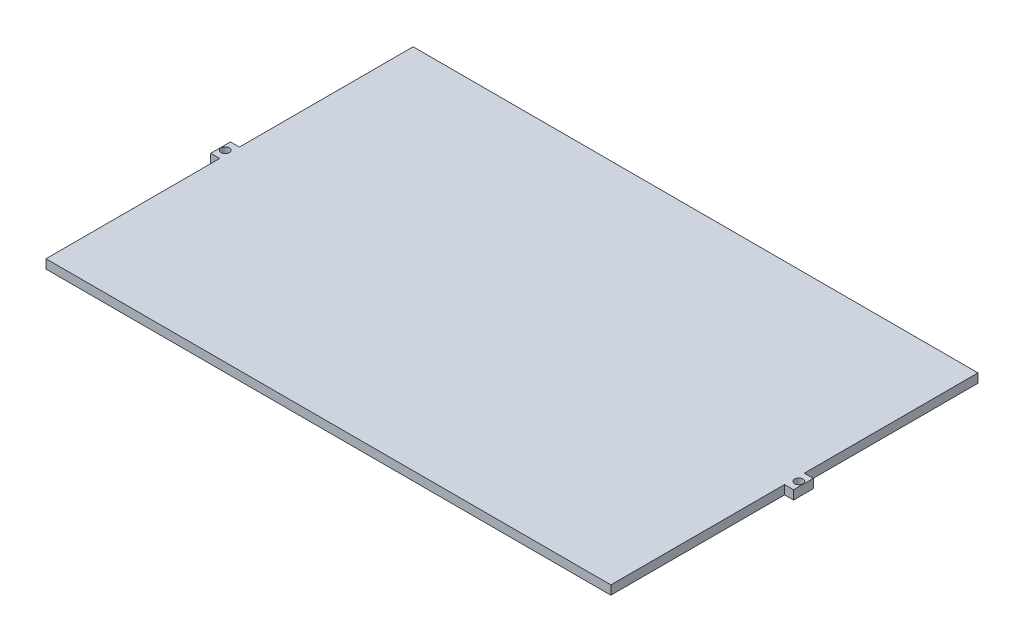
SolidWorks part; units mm, degrees
ref_plane "Front Plane" through (0, 0, 0) normal (0, 0, 1) x (1, 0, 0)
ref_plane "Top Plane" through (0, 0, 0) normal (0, 1, 0) x (1, 0, 0)
ref_plane "Right Plane" through (0, 0, 0) normal (1, 0, 0) x (0, 0, -1)
sketch "Sketch2" plane through (0, 0, 0) normal (0, 1, 0) x (1, 0, 0)
  line L1 (-100, 65) -> (100, 65)
  line L2 (-100, 65) -> (-100, -65)
  line L3 (-100, -65) -> (100, -65)
  line L4 (100, 65) -> (100, -65)
  line L5 (-100, 65) -> (100, -65) construction
  line L6 (-100, -65) -> (100, 65) construction
  point P0 (0, 0)
  dimension "D1" = 200
  dimension "D2" = 130
extrude "Boss-Extrude1" add sketch "Sketch2" along normal blind 3.18
sketch "Sketch5" plane through (-100, 0, 0) normal (-1, 0, 0) x (0, 0, 1)
  line L0 (0, 0) -> (0, 3.18) construction
  line L1 (-65, 0) -> (65, 0) construction
  line L2 (-65, 3.18) -> (65, 3.18) construction
  line L5 (3.5, 0) -> (-3.5, 0)
  line L6 (3.5, 0) -> (3.5, 3.18)
  line L7 (3.5, 3.18) -> (-3.5, 3.18)
  line L8 (-3.5, 0) -> (-3.5, 3.18)
  line L9 (3.5, 0) -> (-3.5, 3.18) construction
  line L10 (3.5, 3.18) -> (-3.5, 0) construction
  point P6 (0, 1.59)
  dimension "D1" = 7
sketch "Sketch7" [suppressed] plane through (0, 0, -65) normal (0, 0, -1) x (-1, 0, 0)
  line L0 (3.5, 0) -> (3.5, 3.18)
  line L1 (3.5, 0) -> (-3.5, 0)
  line L2 (3.5, 3.18) -> (-3.5, 3.18)
  line L3 (-3.5, 0) -> (-3.5, 3.18)
  line L4 (-65, 0) -> (65, 0) construction
  line L5 (-65, 3.18) -> (65, 3.18) construction
  line L7 (65, 3.18) -> (65, 0) construction
  line L8 (-65, 3.18) -> (-65, 0) construction
  line L9 (0, 0) -> (0, 3.18) construction
  dimension "D1" = 7
  dimension "D2" = 3.5
extrude "Cut-Extrude2" [suppressed] cut sketch "Sketch7" against normal blind 3.18
sketch "Sketch8" [suppressed] plane through (0, 0, -61.82) normal (0, 0, -1) x (-1, 0, 0)
  line L0 (0, 0) -> (0, 3.18) construction
  line L1 (-3.5, 0) -> (3.5, 0) construction
  line L2 (3.5, 3.18) -> (-3.5, 3.18) construction
  line L4 (-1.47, 0) -> (1.47, 0)
  line L5 (-1.47, 0) -> (-1.47, 3.18)
  line L6 (-1.47, 3.18) -> (1.47, 3.18)
  line L7 (1.47, 0) -> (1.47, 3.18)
  line L8 (-1.47, 0) -> (1.47, 3.18) construction
  line L9 (-1.47, 3.18) -> (1.47, 0) construction
  point P6 (0, 1.59)
  dimension "D1" = 2.94
extrude "Cut-Extrude3" [suppressed] cut sketch "Sketch8" against normal blind 2.08
sketch "Sketch9" [suppressed] plane through (0, 3.18, 0) normal (0, 1, 0) x (1, 0, 0)
  line L4 (0, 60.1231) -> (0, 52.805) construction
  line L5 (3.25, 57.14) -> (-3.25, 57.14)
  line L6 (3.25, 57.14) -> (3.25, 59.74)
  line L7 (3.25, 59.74) -> (-3.25, 59.74)
  line L8 (-3.25, 57.14) -> (-3.25, 59.74)
  line L10 (-1.47, 59.74) -> (1.47, 59.74) construction
  dimension "D1" = 0
  dimension "D2" = 6.5
  dimension "D3" = 3.25
  dimension "D4" = 2.6
extrude "Cut-Extrude4" [suppressed] cut sketch "Sketch9" against normal through all
sketch "Sketch10" [suppressed] plane through (0, 0, -57.14) normal (0, 0, -1) x (-1, 0, 0)
  line L0 (3.25, 0) -> (-3.25, 0) construction
  line L1 (-1.3107, 0) -> (1.6293, 0)
  line L2 (-1.3107, 0) -> (-1.3107, 3.18)
  line L3 (-1.3107, 3.18) -> (1.6293, 3.18)
  line L4 (1.6293, 0) -> (1.6293, 3.18)
  line L5 (3.25, 3.18) -> (-3.25, 3.18) construction
  dimension "D1" = 2.94
extrude "Boss-Extrude2" add sketch "Sketch5" along normal blind 3.18
sketch "Sketch11" plane through (0, 3.18, 0) normal (0, 1, 0) x (1, 0, 0)
  line L0 (-109.851, 5.029) -> (-100, 5.2135) construction
  line L1 (-100, 65) -> (-100, 3.5) construction
  line L2 (-100, 5.2135) -> (-100, -5.7334) construction
  line L3 (-100, -3.5) -> (-100, -65) construction
  circle A0 centre (-101.55, 0) radius 1.47
  dimension "D1" = 2.94
  dimension "D2" = 1.55
extrude "Cut-Extrude5" cut sketch "Sketch11" against normal blind 3.18 contours A0
mirror "Mirror1" about plane through (0, 0, 0) normal (1, 0, 0) of "Cut-Extrude5", "Boss-Extrude2"
mirror "Mirror2" [suppressed] about plane through (0, 0, 0) normal (0, 0, 1)
pattern_circular "CirPattern1" [suppressed] count 4 over 360
